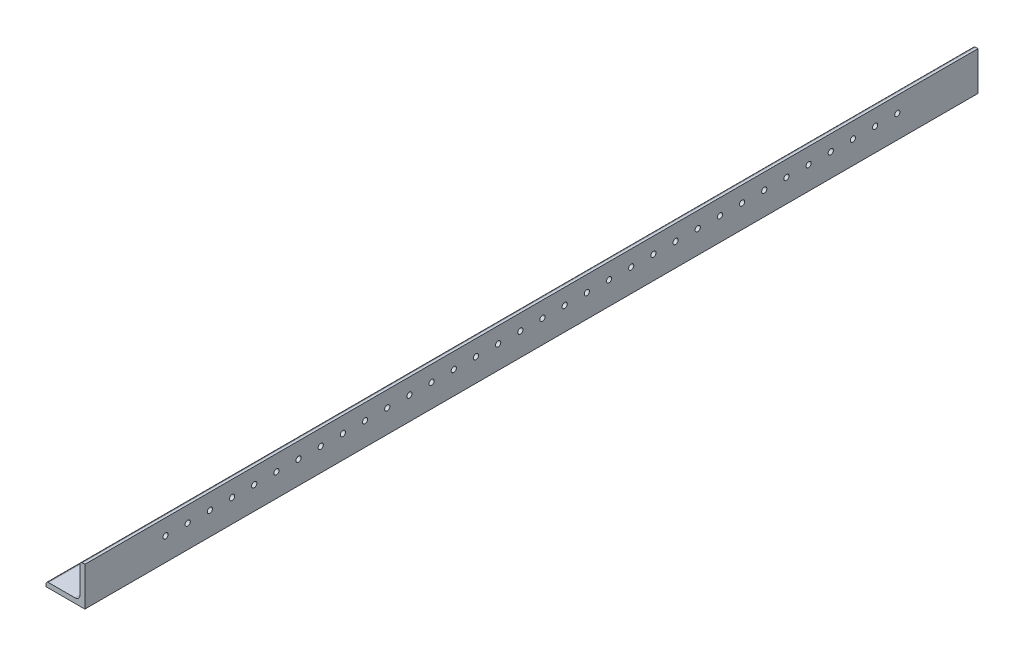
SolidWorks part; units mm, degrees
material "6061-T6 (SS)"
ref_plane "Front Plane" through (0, 0, 0) normal (0, 0, 1) x (1, 0, 0)
ref_plane "Top Plane" through (0, 0, 0) normal (0, 1, 0) x (1, 0, 0)
ref_plane "Right Plane" through (0, 0, 0) normal (1, 0, 0) x (0, 0, -1)
sketch "Sketch0" plane through (0, 0, 0) normal (0, 0, 1) x (1, 0, 0)
  line L0 (-12.7, -12.7) -> (12.7, -12.7)
  line L1 (12.7, -12.7) -> (12.7, 12.7)
  line L2 (12.7, 0) -> (0, 0) construction
  line L3 (0, 0) -> (0, -12.7) construction
  line L4 (9.525, -6.35) -> (9.525, 12.7) construction
  line L5 (6.35, -9.525) -> (-12.7, -9.525) construction
  arc A0 (9.525, -6.35) -> (6.35, -9.525) centre (6.35, -6.35) cw
  point P3 (8.5951, -8.5951)
  dimension "Inside Corner Radius" = 3.175
  dimension "Outside Height" = 25.4
  dimension "Inside Height" = 22.225
  dimension "Inside Width" = 22.225
  dimension "Wall Thickness" = 3.175
  dimension "D1" = 3.175
  dimension "Outside Width" = 25.4
sketch "Sketch1" plane through (0, 0, 0) normal (1, 0, 0) x (0, 0, -1)
  line L0 (609.6, 0) -> (-609.6, 0)
  point P4 (0, 0)
  dimension "Length" = 1219.2
sketch "Sketch2" plane through (0, 0, 0) normal (0, 0, 1) x (1, 0, 0)
  line L0 (-12.7, -12.7) -> (12.7, -12.7)
  line L1 (12.7, -12.7) -> (12.7, 12.7)
  line L2 (12.7, 12.7) -> (9.525, 12.7) construction
  line L3 (9.525, 11.1125) -> (9.525, -6.35)
  line L4 (6.35, -9.525) -> (-11.1125, -9.525)
  line L5 (-12.7, -12.7) -> (-12.7, -9.525) construction
  line L6 (11.1125, 12.7) -> (12.7, 12.7)
  line L7 (-12.7, -11.1125) -> (-12.7, -12.7)
  line L8 (12.7, 0) -> (0, 0) construction
  line L9 (0, 0) -> (0, -12.7) construction
  arc A0 (9.525, 11.1125) -> (11.1125, 12.7) centre (11.1125, 11.1125) cw
  arc A1 (-12.7, -11.1125) -> (-11.1125, -9.525) centre (-11.1125, -11.1125) cw
  arc A2 (9.525, -6.35) -> (6.35, -9.525) centre (6.35, -6.35) cw
  dimension "Inside Radius" = 3.175
  dimension "Height" = 25.4
  dimension "Width" = 25.4
  dimension "Thickness" = 3.175
extrude "Boss-Extrude1" add sketch "Sketch2" along normal mid plane 1219.2
sketch "Break Locations" plane through (0, 0, 0) normal (1, 0, 0) x (0, 0, -1)
  line L0 (-583.692, 0) -> (583.692, 0)
  line L1 (-609.6, -12.7) -> (-609.6, 12.7) construction
  line L2 (609.6, -12.7) -> (609.6, 12.7) construction
  point P0 (-588.01, 0)
  point P1 (588.01, 0)
  point P10 (0, 0)
  point P11 (583.692, 0)
  point P13 (-583.692, 0)
  dimension "D1" = 21.59
  dimension "D2" = 21.59
  dimension "D3" = 25.908
sketch "Sketch3" plane through (12.7, 0, 0) normal (1, 0, 0) x (0, 0, -1)
  line L0 (-609.6, -12.7) -> (609.6, -12.7) construction
  line L1 (609.6, 12.7) -> (-25.6, 12.7)
  line L2 (609.6, 12.7) -> (609.6, -12.7)
  line L3 (609.6, -12.7) -> (-25.6, -12.7)
  line L4 (-25.6, 12.7) -> (-25.6, -12.7)
  line L5 (-609.6, -12.7) -> (-609.6, 12.7) construction
  dimension "D1" = 584
extrude "Cut-Extrude2" cut sketch "Sketch3" against normal blind 30.48
sketch "Sketch5" plane through (9.525, 0, 0) normal (-1, 0, 0) x (0, 0, 1)
  line L0 (562.77, 11.1125) -> (562.77, -6.35) construction
  line L1 (609.6, 11.1125) -> (25.6, 11.1125) construction
  line L2 (609.6, 11.1125) -> (609.6, -6.35) construction
  line L3 (609.6, -6.35) -> (25.6, -6.35) construction
  line L4 (72.43, 11.1125) -> (72.43, -6.35) construction
  line L6 (72.43, 2.3812) -> (562.77, 2.3812) construction
  line L7 (78.35, 2.3812) -> (72.43, 2.3812)
  line L8 (556.85, 2.3812) -> (562.77, 2.3812)
  line L9 (72.43, 8.7325) -> (72.43, -3.9675) construction
  circle A0 centre (78.35, 2.3812) radius 1.7
  circle A1 centre (92.85, 2.3812) radius 1.7
  circle A2 centre (107.35, 2.3812) radius 1.7
  circle A3 centre (121.85, 2.3812) radius 1.7
  circle A4 centre (136.35, 2.3812) radius 1.7
  circle A5 centre (150.85, 2.3812) radius 1.7
  circle A6 centre (165.35, 2.3812) radius 1.7
  circle A7 centre (179.85, 2.3812) radius 1.7
  circle A8 centre (194.35, 2.3812) radius 1.7
  circle A9 centre (208.85, 2.3812) radius 1.7
  circle A10 centre (223.35, 2.3812) radius 1.7
  circle A11 centre (237.85, 2.3812) radius 1.7
  circle A12 centre (252.35, 2.3812) radius 1.7
  circle A13 centre (266.85, 2.3812) radius 1.7
  circle A14 centre (281.35, 2.3812) radius 1.7
  circle A15 centre (295.85, 2.3812) radius 1.7
  circle A16 centre (310.35, 2.3812) radius 1.7
  circle A17 centre (324.85, 2.3812) radius 1.7
  circle A18 centre (339.35, 2.3812) radius 1.7
  circle A19 centre (353.85, 2.3812) radius 1.7
  circle A20 centre (368.35, 2.3812) radius 1.7
  circle A21 centre (382.85, 2.3812) radius 1.7
  circle A22 centre (397.35, 2.3812) radius 1.7
  circle A23 centre (411.85, 2.3812) radius 1.7
  circle A24 centre (426.35, 2.3812) radius 1.7
  circle A25 centre (440.85, 2.3812) radius 1.7
  circle A26 centre (455.35, 2.3812) radius 1.7
  circle A27 centre (469.85, 2.3812) radius 1.7
  circle A28 centre (484.35, 2.3812) radius 1.7
  circle A29 centre (498.85, 2.3812) radius 1.7
  circle A30 centre (513.35, 2.3812) radius 1.7
  circle A31 centre (527.85, 2.3812) radius 1.7
  circle A32 centre (542.35, 2.3812) radius 1.7
  circle A33 centre (556.85, 2.3812) radius 1.7
  dimension "D1" = 3.4
  dimension "D3" = 14.5
  dimension "D4" = 46.83
  dimension "D2" = 34
extrude "Cut-Extrude3" cut sketch "Sketch5" against normal through all
sketch "Sketch7" plane through (0, -9.525, 0) normal (0, 1, 0) x (1, 0, 0)
  line L0 (-11.1125, -562.7675) -> (6.35, -562.7675) construction
  line L1 (-11.1125, -609.6) -> (-11.1125, -25.6) construction
  line L2 (-2.3812, -556.85) -> (-2.3812, -562.7675)
  line L3 (6.35, -609.6) -> (6.35, -25.6) construction
  line L4 (6.35, -25.6) -> (-11.1125, -25.6) construction
  line L5 (-2.3812, -72.4325) -> (-2.3812, -562.7675) construction
  line L6 (-2.3813, -78.35) -> (-2.3812, -72.4325)
  line L7 (6.35, -609.6) -> (-11.1125, -609.6) construction
  circle A0 centre (-2.3813, -78.35) radius 1.7
  circle A1 centre (-2.3812, -92.85) radius 1.7
  circle A2 centre (-2.3812, -107.35) radius 1.7
  circle A3 centre (-2.3812, -121.85) radius 1.7
  circle A4 centre (-2.3812, -136.35) radius 1.7
  circle A5 centre (-2.3812, -150.85) radius 1.7
  circle A6 centre (-2.3812, -165.35) radius 1.7
  circle A7 centre (-2.3812, -179.85) radius 1.7
  circle A8 centre (-2.3812, -194.35) radius 1.7
  circle A9 centre (-2.3812, -208.85) radius 1.7
  circle A10 centre (-2.3812, -223.35) radius 1.7
  circle A11 centre (-2.3812, -237.85) radius 1.7
  circle A12 centre (-2.3812, -252.35) radius 1.7
  circle A13 centre (-2.3812, -266.85) radius 1.7
  circle A14 centre (-2.3812, -281.35) radius 1.7
  circle A15 centre (-2.3812, -295.85) radius 1.7
  circle A16 centre (-2.3812, -310.35) radius 1.7
  circle A17 centre (-2.3812, -324.85) radius 1.7
  circle A18 centre (-2.3812, -339.35) radius 1.7
  circle A19 centre (-2.3812, -353.85) radius 1.7
  circle A20 centre (-2.3812, -368.35) radius 1.7
  circle A21 centre (-2.3812, -382.85) radius 1.7
  circle A22 centre (-2.3812, -397.35) radius 1.7
  circle A23 centre (-2.3812, -411.85) radius 1.7
  circle A24 centre (-2.3812, -426.35) radius 1.7
  circle A25 centre (-2.3812, -440.85) radius 1.7
  circle A26 centre (-2.3812, -455.35) radius 1.7
  circle A27 centre (-2.3812, -469.85) radius 1.7
  circle A28 centre (-2.3812, -484.35) radius 1.7
  circle A29 centre (-2.3812, -498.85) radius 1.7
  circle A30 centre (-2.3812, -513.35) radius 1.7
  circle A31 centre (-2.3812, -527.85) radius 1.7
  circle A32 centre (-2.3812, -542.35) radius 1.7
  circle A33 centre (-2.3812, -556.85) radius 1.7
  dimension "D2" = 3.4
  dimension "D3" = 14.5
  dimension "D4" = 46.8325
  dimension "D5" = 46.8325
  dimension "D1" = 34
extrude "Cut-Extrude4" cut sketch "Sketch7" against normal through all
equation "\"D1@Break Locations\" = .85 * \"Height@Sketch2\""
equation "\"D2@Break Locations\"=\"D1@Break Locations\""
equation "\"Thickness@Sketch2\" = \"Wall Thickness@Sketch0\""
equation "\"Height@Sketch2\" = \"Outside Height@Sketch0\""
equation "\"Width@Sketch2\" = \"Outside Width@Sketch0\""
equation "\"Inside Radius@Sketch2\" = \"Inside Corner Radius@Sketch0\""
equation "\"Length@Boss-Extrude1\" = \"Length@Sketch1\""
equation "\"D3@Break Locations\"=\"D2@Break Locations\"*1.2"
equation "\"D1@Sketch0\"=\"Wall Thickness@Sketch0\""
